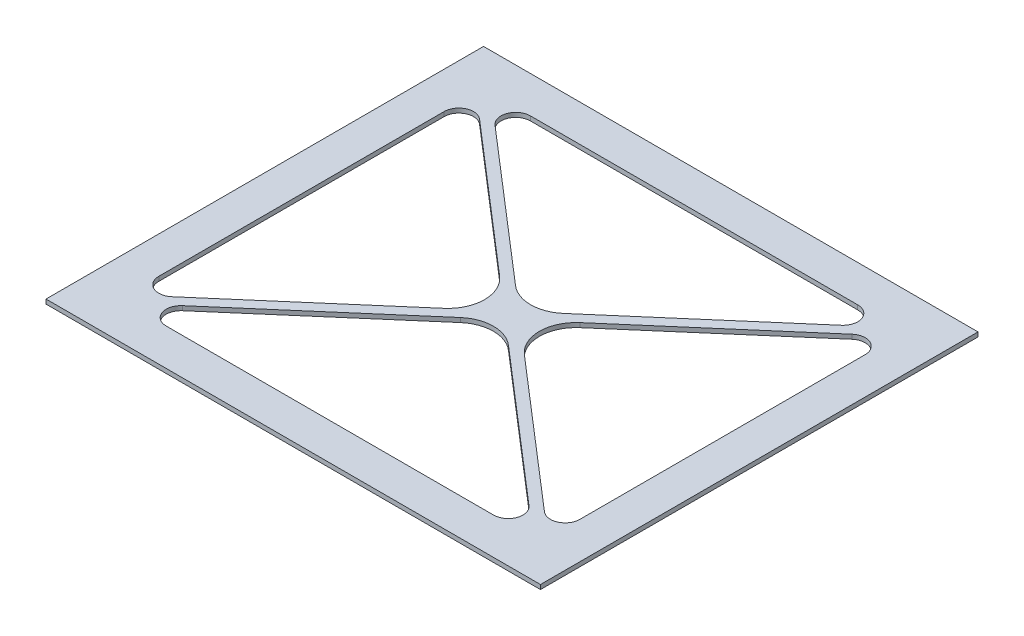
SolidWorks part; units mm, degrees
ref_plane "Front Plane" through (0, 0, 0) normal (0, 0, 1) x (1, 0, 0)
ref_plane "Top Plane" through (0, 0, 0) normal (0, 1, 0) x (1, 0, 0)
ref_plane "Right Plane" through (0, 0, 0) normal (1, 0, 0) x (0, 0, -1)
sketch "Sketch1" plane through (0, 0, 0) normal (0, 1, 0) x (1, 0, 0)
  line L0 (122.7, 109.2) -> (67.35, 61.4625)
  line L1 (0, 0) -> (134.7, 0)
  line L2 (0, 0) -> (0, 119.2)
  line L3 (0, 119.2) -> (134.7, 119.2)
  line L4 (134.7, 0) -> (134.7, 119.2)
  line L5 (12, 109.2) -> (122.7, 109.2)
  line L6 (10, 107.2) -> (10, 12)
  line L7 (12, 10) -> (122.7, 10)
  line L8 (124.7, 107.2) -> (124.7, 12)
  line L10 (12, 10) -> (67.35, 57.7375)
  line L11 (122.7, 10) -> (67.35, 57.7375)
  line L12 (12, 109.2) -> (67.35, 61.4625)
  line L13 (65.1905, 59.6) -> (10, 12)
  line L14 (69.5095, 59.6) -> (124.7, 107.2)
  line L15 (69.5095, 59.6) -> (124.7, 12)
  line L16 (65.1905, 59.6) -> (10, 107.2)
  dimension "D1" = 134.7
  dimension "D2" = 119.2
  dimension "D3" = 10
  dimension "D4" = 10
  dimension "D5" = 10
  dimension "D6" = 10
extrude "Boss-Extrude1" add sketch "Sketch1" along normal blind 1.2
fillet "Fillet1" radius 10 4 edges at (65.1905, 0.6, -59.6) (67.35, 0.6, -61.4625) (69.5095, 0.6, -59.6) (67.35, 0.6, -57.7375)
fillet "Fillet2" radius 4 8 edges at (122.7, 0.6, -10) (124.7, 0.6, -12) (124.7, 0.6, -107.2) (122.7, 0.6, -109.2) (12, 0.6, -109.2) (10, 0.6, -107.2) (10, 0.6, -12) (12, 0.6, -10)
